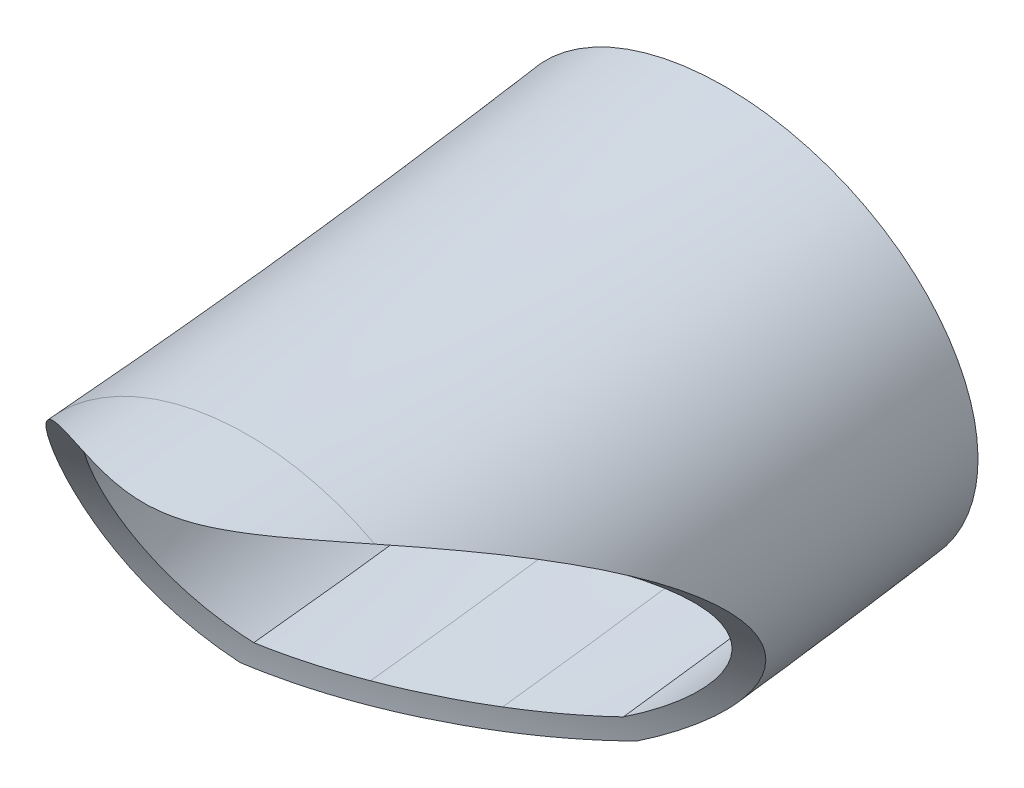
SolidWorks part; units mm, degrees
ref_plane "Front Plane" through (0, 0, 0) normal (0, 0, 1) x (1, 0, 0)
ref_plane "Top Plane" through (0, 0, 0) normal (0, 1, 0) x (1, 0, 0)
ref_plane "Right Plane" through (0, 0, 0) normal (1, 0, 0) x (0, 0, -1)
sketch "Sketch1" plane through (0, 0, 0) normal (0, 0, 1) x (1, 0, 0)
  ellipse E1 centre (-697.9953, 47.3432) end of major axis (-707.4613, 46.5405) minor radius 7.8603 (-693.35, 40.605) -> (-704.2388, 41.251) ccw construction
  ellipse E2 centre (-697.9953, 47.3432) end of major axis (-707.4613, 46.5405) minor radius 7.8603 (-693.35, 40.605) -> (-704.2388, 41.251) ccw construction
  spline S0 degree 1 poles (-693.2528, 40.3185) (-704.3765, 40.9814) knots 0 0 1 1 construction
  spline S1 degree 1 poles (-704.3765, 40.9814) (-700.9126, 40.1612) knots 0 0 1 1 construction
  spline S2 degree 1 poles (-700.9126, 40.1612) (-696.9471, 39.9259) knots 0 0 1 1 construction
  spline S3 degree 1 poles (-696.9471, 39.9259) (-693.2528, 40.3185) knots 0 0 1 1 construction
  spline S4 degree 3 poles (-3699.5803, -44.3284) (-617.0858, 48.0374) (-716.6851, 42.4375) (-700.3201, 40.3853) (-700.1664, 40.3674) (-699.8372, 40.333) (-699.6648, 40.3167) (-699.2993, 40.2867) (-699.1093, 40.2732) (-698.7316, 40.2509) (-698.5391, 40.2418) (-698.1747, 40.2287) (-697.9982, 40.2244) (-676.9712, 39.921) (-818.2821, 68.216) (2201.1488, -734.4424) knots -13.986788 -13.986788 -13.986788 -13.986788 0.125 0.125 0.25 0.25 0.375 0.375 0.5 0.5 0.625 0.625 0.75 0.75 16.589538 16.589538 16.589538 16.589538 only from (-700.8698, 40.4581) to (-696.9539, 40.2258) construction
  spline S5 degree 3 poles (-700.8698, 40.4581) (-700.742, 40.4396) (-700.6074, 40.4213) (-700.3201, 40.3853) (-700.1664, 40.3674) (-699.8372, 40.333) (-699.6648, 40.3167) (-699.2993, 40.2867) (-699.1093, 40.2732) (-698.7316, 40.2509) (-698.5391, 40.2418) (-698.1747, 40.2287) (-697.9982, 40.2244) (-697.5043, 40.2173) (-697.2154, 40.2197) (-696.9539, 40.2258) knots 0 0 0 0 0.125 0.125 0.25 0.25 0.375 0.375 0.5 0.5 0.625 0.625 0.75 0.75 1 1 1 1 construction
  spline S6 degree 3 poles (-3701.7003, 161.758) (-598.7187, 47.2176) (-722.1512, 46.6452) (-703.435, 40.9946) (-703.2021, 40.9292) (-702.6812, 40.7972) (-702.3927, 40.7302) (-701.8913, 40.6288) (-701.7128, 40.5949) (-689.6479, 38.4919) (-617.3703, 35.8838) (2298.6942, 7.8913) knots -21.376355 -21.376355 -21.376355 -21.376355 0.25 0.25 0.5 0.5 0.75 0.75 0.875 0.875 8.469221 8.469221 8.469221 8.469221 only from (-704.2388, 41.251) to (-700.8698, 40.4581) construction
  spline S7 degree 3 poles (-704.2388, 41.251) (-704.0577, 41.1876) (-703.8628, 41.1237) (-703.435, 40.9946) (-703.2021, 40.9292) (-702.6812, 40.7972) (-702.3927, 40.7302) (-701.8913, 40.6288) (-701.7128, 40.5949) (-701.3221, 40.5268) (-701.1103, 40.4926) (-700.8698, 40.4581) knots 0 0 0 0 0.25 0.25 0.5 0.5 0.75 0.75 0.875 0.875 1 1 1 1 construction
  spline S8 degree 3 poles (-3679.8602, 359.4726) (-780.2342, 45.4565) (-708.6345, 39.6251) (-696.0778, 40.2604) (-695.8907, 40.2725) (-695.3626, 40.3126) (-695.0541, 40.3441) (-694.4923, 40.412) (-694.2388, 40.4484) (-673.6402, 43.7831) (-794.5719, 59.0027) (2297.114, -196.8709) knots -7.451151 -7.451151 -7.451151 -7.451151 0.125 0.125 0.25 0.25 0.5 0.5 0.75 0.75 22.410738 22.410738 22.410738 22.410738 only from (-696.9539, 40.2258) to (-693.35, 40.605) construction
  spline S9 degree 3 poles (-696.9539, 40.2258) (-696.7054, 40.2312) (-696.4854, 40.2398) (-696.0778, 40.2604) (-695.8907, 40.2725) (-695.3626, 40.3126) (-695.0541, 40.3441) (-694.4923, 40.412) (-694.2388, 40.4484) (-693.7688, 40.5245) (-693.5525, 40.5642) (-693.35, 40.605) knots 0 0 0 0 0.125 0.125 0.25 0.25 0.5 0.5 0.75 0.75 1 1 1 1 construction
  spline S10 degree 3 poles (-693.2528, 40.3185) (-692.8079, 40.5355) (-691.94, 41.0361) (-690.42, 42.239) (-688.9589, 44.0883) (-688.1057, 46.6429) (-688.2877, 50.1566) (-691.0052, 54.025) (-696.9358, 56.0506) (-703.2608, 54.7491) (-706.8633, 51.2849) (-707.9083, 47.856) (-707.6988, 45.2287) (-706.7079, 43.2199) (-705.4998, 41.8478) (-704.7619, 41.2478) (-704.3765, 40.9814) knots 2.008162 2.008162 2.008162 2.008162 2.166359 2.324555 2.640947 2.957339 3.273732 3.906516 4.539301 5.172086 5.80487 6.121263 6.437655 6.754047 6.912244 7.07044 7.07044 7.07044 7.07044
  spline S11 degree 3 poles (-704.3765, 40.9814) (-704.1757, 40.9111) (-703.7966, 40.7852) (-703.0696, 40.5798) (-702.333, 40.4076) (-701.687, 40.2845) (-701.2727, 40.2148) (-701.0298, 40.178) (-700.9126, 40.1612) knots -0.017712 -0.017712 -0.017712 -0.017712 0.236706 0.491125 0.745543 0.872752 0.936357 0.999961 0.999961 0.999961 0.999961
  spline S12 degree 3 poles (-700.9126, 40.1612) (-700.7755, 40.1413) (-700.5138, 40.1059) (-699.8871, 40.0328) (-698.9399, 39.9531) (-697.9837, 39.9206) (-697.3556, 39.9186) (-697.087, 39.9226) (-696.9471, 39.9259) knots 0.000072 0.000072 0.000072 0.000072 0.125055 0.250037 0.500001 0.749966 0.874948 0.99993 0.99993 0.99993 0.99993
  spline S13 degree 3 poles (-696.9471, 39.9259) (-696.8262, 39.9285) (-696.5756, 39.936) (-696.1454, 39.9553) (-695.4704, 39.9994) (-694.6849, 40.0806) (-693.8961, 40.1953) (-693.4752, 40.2737) (-693.2528, 40.3185) knots 0.000037 0.000037 0.000037 0.000037 0.063511 0.126985 0.253933 0.50783 0.761726 1.015623 1.015623 1.015623 1.015623
  spline S14 degree 1 poles (-692.9325, 39.3629) (-704.8308, 40.0809) knots 0 0 1 1 construction
  spline S15 degree 1 poles (-704.8308, 40.0809) (-701.0552, 39.1714) knots 0 0 1 1 construction
  spline S16 degree 1 poles (-701.0552, 39.1714) (-696.9245, 38.9261) knots 0 0 1 1 construction
  spline S17 degree 1 poles (-696.9245, 38.9261) (-692.9325, 39.3629) knots 0 0 1 1 construction
  spline S18 degree 3 poles (-692.9325, 39.3629) (-691.957, 39.8254) (-690.0995, 41.0465) (-688.1128, 43.5107) (-687.0984, 46.4265) (-687.235, 49.4709) (-688.5071, 52.2669) (-691.4671, 55.2566) (-696.8864, 57.1004) (-703.7639, 55.679) (-707.7701, 51.8234) (-708.9379, 47.887) (-708.6593, 44.8535) (-707.4905, 42.5672) (-706.1008, 41.0332) (-705.267, 40.3738) (-704.8308, 40.0809) knots 1.995536 1.995536 1.995536 1.995536 2.313581 2.631626 2.949671 3.267716 3.585761 3.903806 4.539896 5.175987 5.812077 6.130122 6.448167 6.766212 6.925235 7.084257 7.084257 7.084257 7.084257
  spline S19 degree 3 poles (-704.8308, 40.0809) (-704.7286, 40.0451) (-704.5337, 39.9761) (-704.0648, 39.8232) (-703.5464, 39.6734) (-702.9321, 39.5205) (-702.4093, 39.4048) (-701.9051, 39.3075) (-701.4516, 39.2306) (-701.1841, 39.1899) (-701.0552, 39.1714) knots -0.074723 -0.074723 -0.074723 -0.074723 0.059598 0.193918 0.462559 0.596879 0.731199 0.86552 0.93268 0.99984 0.99984 0.99984 0.99984
  spline S20 degree 3 poles (-701.0552, 39.1714) (-700.9119, 39.1507) (-700.6379, 39.1136) (-699.9842, 39.0373) (-698.9987, 38.9545) (-698.0047, 38.9206) (-697.3507, 38.9186) (-697.0704, 38.9227) (-696.9245, 38.9261) knots 0.0003 0.0003 0.0003 0.0003 0.125226 0.250152 0.500005 0.749857 0.874783 0.999709 0.999709 0.999709 0.999709
  spline S21 degree 3 poles (-696.9245, 38.9261) (-696.7926, 38.929) (-696.519, 38.9373) (-696.0519, 38.9588) (-695.5295, 38.9939) (-694.9811, 39.0445) (-694.3291, 39.1202) (-693.7712, 39.2041) (-693.2632, 39.2958) (-693.0457, 39.3401) (-692.9325, 39.3629) knots 0.000154 0.000154 0.000154 0.000154 0.06678 0.133406 0.266658 0.39991 0.533162 0.799666 0.932918 1.06617 1.06617 1.06617 1.06617
  point P1 (-693.3306, 40.6145)
  point P18 (-704.2391, 41.2512)
  dimension "D1" = 0.3
  dimension "D2" = 1.3
ref_plane "Plane1" through (-698.3791, 41.4365, 0) normal (0.9982, -0.0592, 0) x (0, 0, -1)
sketch "Sketch2" plane through (-698.3791, 41.4365, 0) normal (0.9982, -0.0592, 0) x (0, 0, -1)
  line L0 (7.6596, 7.5591) -> (0, 6.8766) construction
  line L1 (7.6596, 7.5591) -> (0, 6.8766)
  arc A0 (7.6596, 7.5591) -> (29.6716, 10.5107) centre (-14.5274, 256.5726) ccw construction
  arc A1 (7.6596, 7.5591) -> (29.6716, 10.5107) centre (-14.5274, 256.5726) ccw
sweep "Sweep1" add profiles "Sketch1" path "Sketch2"
sketch "Sketch3" plane through (-577.6757, 56.5027, 287.1066) normal (-0.8921, 0.0873, 0.4434) x (0.4413, -0.0432, 0.8963)
  circle A0 centre (-309.4381, -27.2324) radius 16.25 construction
  circle A1 centre (-309.4381, -27.2324) radius 16.25
extrude "Cut-Extrude1" cut sketch "Sketch3" against normal through all
